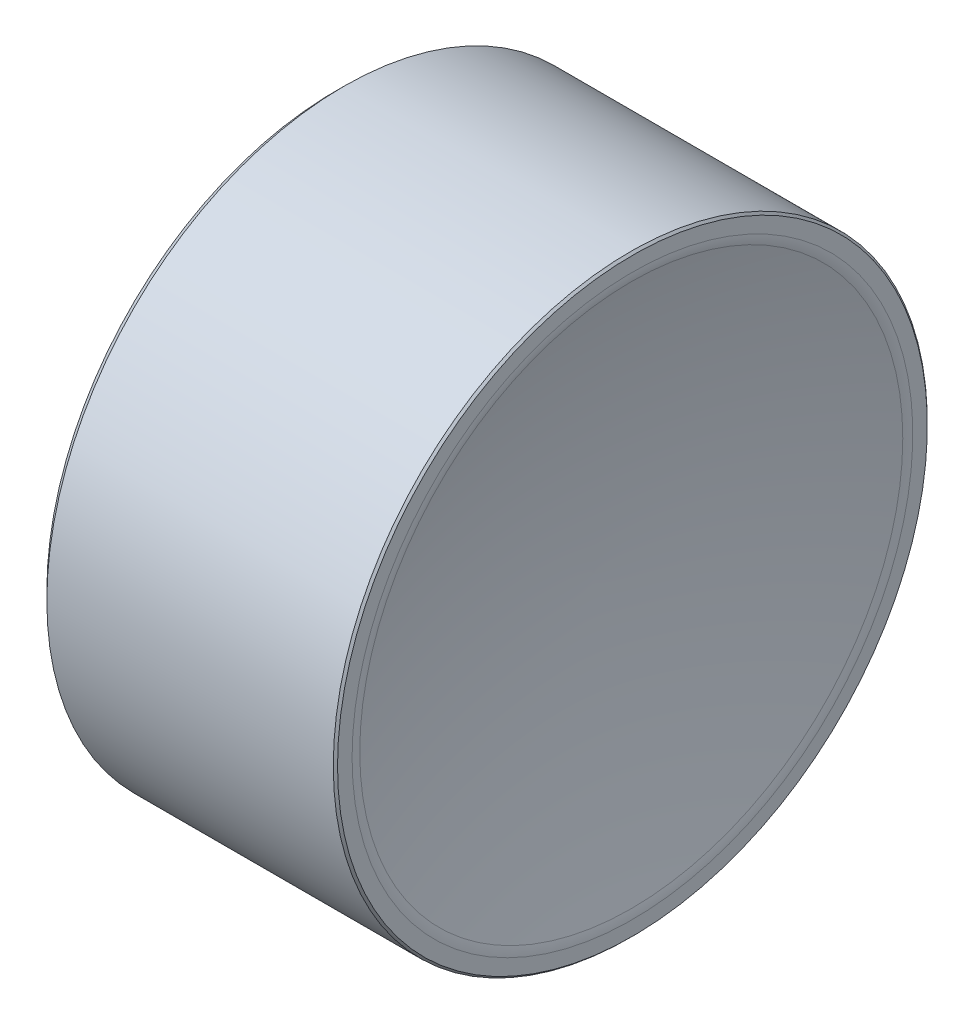
SolidWorks part; units mm, degrees
material "AISI 304"
ref_plane "Front Plane" through (0, 0, 0) normal (0, 0, 1) x (1, 0, 0)
ref_plane "Top Plane" through (0, 0, 0) normal (0, 1, 0) x (1, 0, 0)
ref_plane "Right Plane" through (0, 0, 0) normal (1, 0, 0) x (0, 0, -1)
sketch "Sketch1" plane through (0, 0, 0) normal (0, 0, 1) x (1, 0, 0)
  line L0 (-2.6213, 22.225) -> (-1.2946, 22.225)
  line L1 (0, 42.8625) -> (-20.6375, 42.8625)
  line L2 (-20.6375, 42.8625) -> (-20.6375, 44.45)
  line L3 (-20.6375, 44.45) -> (1.5875, 44.45)
  line L4 (1.5875, 44.45) -> (1.5875, 22.225) construction
  line L6 (1.5875, 44.45) -> (1.5875, 42.8625)
  line L7 (-12.1728, 22.225) -> (11.534, 22.225) construction
  line L8 (0, 22.225) -> (0, 42.8625) construction
  arc A0 (-2.6213, 22.225) -> (0, 42.8625) centre (79.9287, 22.225) cw
  arc A2 (-1.2946, 22.225) -> (1.5875, 42.8625) centre (79.7195, 21.4312) cw
  dimension "D1" = 22.225
  dimension "D5" = 82.55
  dimension "D2" = 1.5875
  dimension "D3" = 22.225
revolve "Revolve1" add sketch "Sketch1" angle 360 about L0
chamfer "Chamfer2" distance 0.635 angle 45 1 edges at (-20.6375, 22.225, 22.225)
chamfer "Chamfer3" distance 0.1588 angle 45 2 edges at (-20.6375, 22.225, 20.6375) (1.5875, 22.225, 22.225)
fillet "Fillet1" radius 2.54 1 edges at (1.5875, 22.225, 20.6375)
fillet "Fillet2" radius 0.635 1 edges at (0, 22.225, 20.6375)
